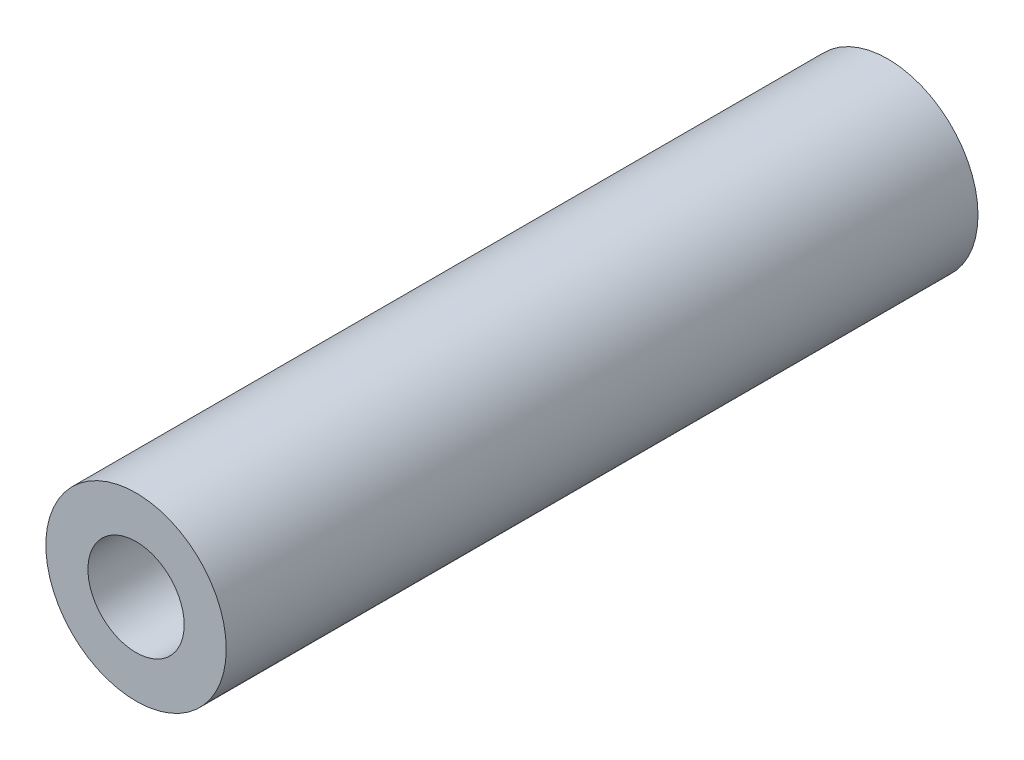
SolidWorks part; units mm, degrees
material "ABS"
ref_plane "Front Plane" through (0, 0, 0) normal (0, 0, 1) x (1, 0, 0)
ref_plane "Top Plane" through (0, 0, 0) normal (0, 1, 0) x (1, 0, 0)
ref_plane "Right Plane" through (0, 0, 0) normal (1, 0, 0) x (0, 0, -1)
sketch "Sketch1" plane through (0, 0, 0) normal (0, 0, 1) x (1, 0, 0)
  line L0 (0, 1.6) -> (0, 3) construction
  line L1 (0, -1.6) -> (0, -3) construction
  circle A0 centre (0, 0) radius 3
  circle A1 centre (0, 0) radius 1.6
  dimension "OD" = 6
  dimension "ID" = 3.2
sketch "Sketch2" plane through (0, 0, 0) normal (1, 0, 0) x (0, 0, -1)
  line L0 (-12.5, 1.6) -> (12.5, 1.6) construction
  line L1 (-12.5, -1.6) -> (12.5, -1.6) construction
  line L2 (-12.5, -3) -> (12.5, -3) construction
  line L3 (-12.5, 3) -> (12.5, 3) construction
  dimension "Length" = 25
extrude "Extrude1" add sketch "Sketch1" along normal up to vertex (12.5 mm away) and the other way up to vertex (12.5 mm away) up to point (0, 1.6, 12.5) other way up to point (0, 1.6, -12.5)
sketch "Sketch3" plane through (0, 0, 12.5) normal (0, 0, 1) x (1, 0, 0)
  circle A0 centre (0, 0) radius 1.6 construction
  circle A3 centre (0, 0) radius 1.6
  point P3 (-1.6, 0)
